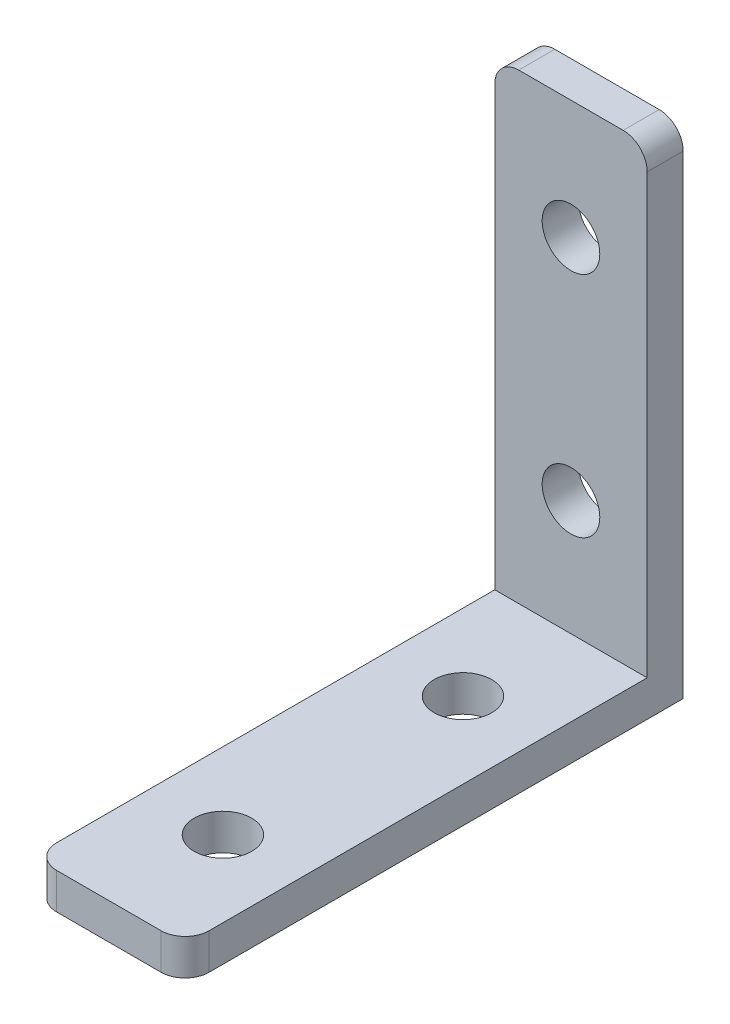
SolidWorks part; units mm, degrees
material "Gerais  - 6061-T6"
ref_plane "Plano frontal" through (0, 0, 0) normal (0, 0, 1) x (1, 0, 0)
ref_plane "Plano superior" through (0, 0, 0) normal (0, 1, 0) x (1, 0, 0)
ref_plane "Plano direito" through (0, 0, 0) normal (1, 0, 0) x (0, 0, -1)
sketch "Esboço1" plane through (0, 0, 0) normal (0, 0, 1) x (1, 0, 0)
  line L1 (-6.35, -20.75) -> (6.35, -20.75)
  line L2 (-6.35, -20.75) -> (-6.35, 20.75)
  line L3 (-6.35, 20.75) -> (6.35, 20.75)
  line L4 (6.35, -20.75) -> (6.35, 20.75)
  line L5 (0, 20.75) -> (0, -20.75) construction
  line L6 (-6.35, 0) -> (6.35, 0) construction
  circle A0 centre (0, 10.85) radius 2.4
  circle A1 centre (0, -8.15) radius 2.4
  point P0 (0, 0)
  dimension "D1" = 4.8
  dimension "D2" = 19
  dimension "D3" = 12.6
  dimension "D4" = 41.5
  dimension "D5" = 12.7
extrude "Ressalto-extrusão1" add sketch "Esboço1" along normal blind 3
sketch "Esboço2" plane through (0, 0, 3) normal (0, 0, 1) x (1, 0, 0)
  line L0 (-6.35, -20.75) -> (6.35, -20.75) construction
  line L1 (6.35, -17.75) -> (-6.35, -17.75)
  line L2 (6.35, -17.75) -> (6.35, -20.75)
  line L3 (6.35, -20.75) -> (-6.35, -20.75)
  line L4 (-6.35, -17.75) -> (-6.35, -20.75)
  line L5 (0, -20.75) -> (0, -17.75) construction
  line L6 (6.35, -19.25) -> (-6.35, -19.25) construction
  point P0 (0, -19.25)
  dimension "D1" = 3
extrude "Ressalto-extrusão2" add sketch "Esboço2" along normal blind 38.5 contours L1 L4 L3 L2
sketch "Esboço3" plane through (0, -17.75, 0) normal (0, 1, 0) x (1, 0, 0)
  line L0 (6.35, -41.5) -> (-6.35, -41.5) construction
  line L2 (-6.35, 0) -> (6.35, 0) construction
  circle A0 centre (0, -12) radius 2.4
  circle A1 centre (0, -32) radius 2.4
  point P5 (0, -41.5)
  point P6 (-11.4915, 0)
  dimension "D1" = 4.8
  dimension "D3" = 20
  dimension "D2" = 12
extrude "Corte-extrusão1" cut sketch "Esboço3" against normal blind 41.5 contours A0 | A1
fillet "Filete1" radius 2 4 edges at (-6.35, 20.75, 1.5) (6.35, 20.75, 1.5) (-6.35, -19.25, 41.5) (6.35, -19.25, 41.5)
